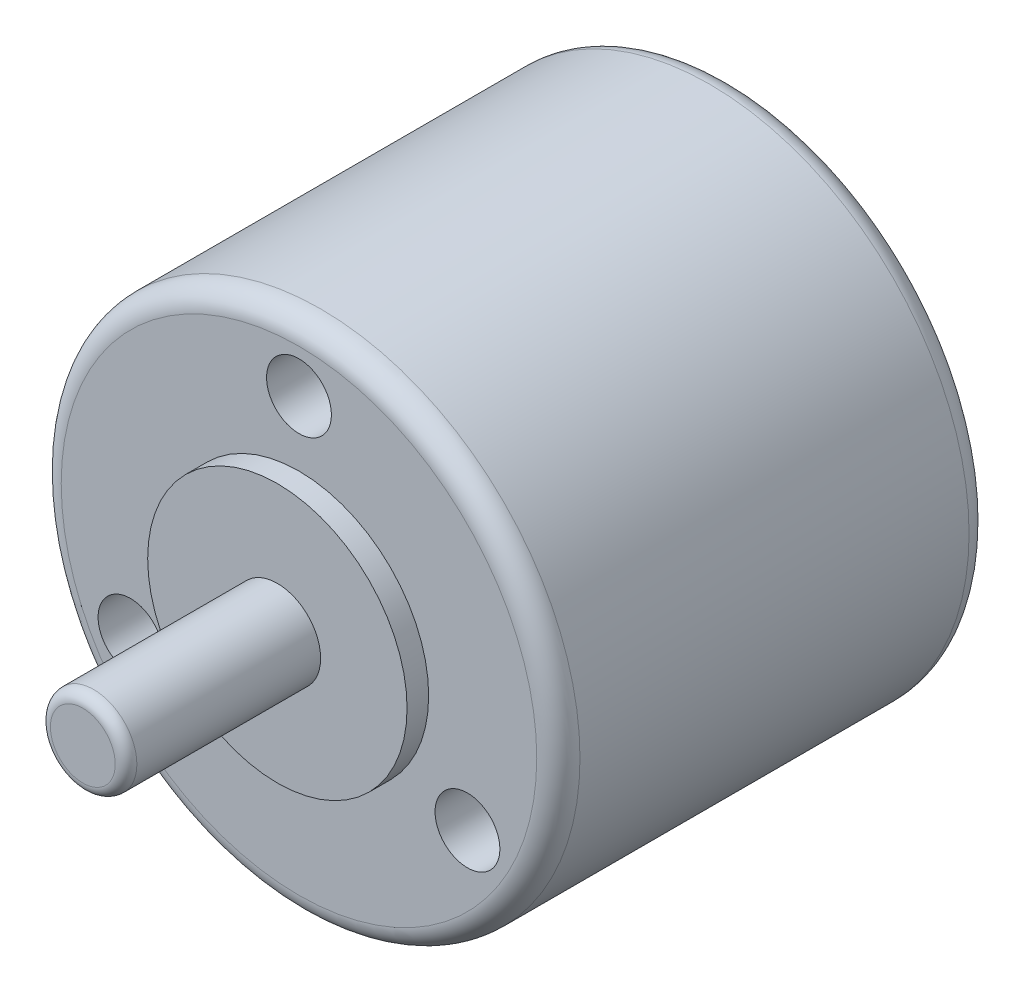
SolidWorks part; units mm, degrees
ref_plane "Plan de face" through (0, 0, 0) normal (0, 0, 1) x (1, 0, 0)
ref_plane "Plan de dessus" through (0, 0, 0) normal (0, 1, 0) x (1, 0, 0)
ref_plane "Plan de droite" through (0, 0, 0) normal (1, 0, 0) x (0, 0, -1)
sketch "Esquisse1" plane through (0, 0, 0) normal (0, 0, 1) x (1, 0, 0)
  circle A0 centre (0, 0) radius 12
extrude "Extrusion1" add sketch "Esquisse1" against normal blind 20
sketch "Esquisse2" plane through (0, 0, 0) normal (0, 0, 1) x (1, 0, 0)
  circle A0 centre (0, 0) radius 2
extrude "Extrusion2" add sketch "Esquisse2" along normal blind 10
fillet "Congé1" radius 1 1 edges at (12, 0, 0)
fillet "Congé2" radius 1 1 edges at (12, 0, -20)
fillet "Congé3" radius 0.5 1 edges at (2, 0, 10)
sketch "Esquisse4" plane through (0, 0, 0) normal (0, 0, 1) x (1, 0, 0)
  circle A0 centre (0, 0) radius 6
extrude "Extrusion3" add sketch "Esquisse4" along normal blind 1
sketch "Esquisse5" plane through (0, 0, 0) normal (0, 0, 1) x (1, 0, 0)
  line L0 (0, 0) -> (0, 9) construction
  line L1 (-7.7942, -4.5) -> (0, 0) construction
  line L2 (0, 0) -> (7.7942, -4.5) construction
  circle A0 centre (0, 9) radius 1.5
  circle A2 centre (-7.7942, -4.5) radius 1.5
  circle A3 centre (7.7942, -4.5) radius 1.5
  dimension "D2" = 9
  dimension "D1" = 9
  dimension "D4" = 3
  dimension "D5" = 3
  dimension "D6" = 3
  dimension "D3" = 9
  dimension "D7" = 120
  dimension "D8" = 120
extrude "Enlèv. mat.-Extru.1" cut sketch "Esquisse5" against normal blind 5
